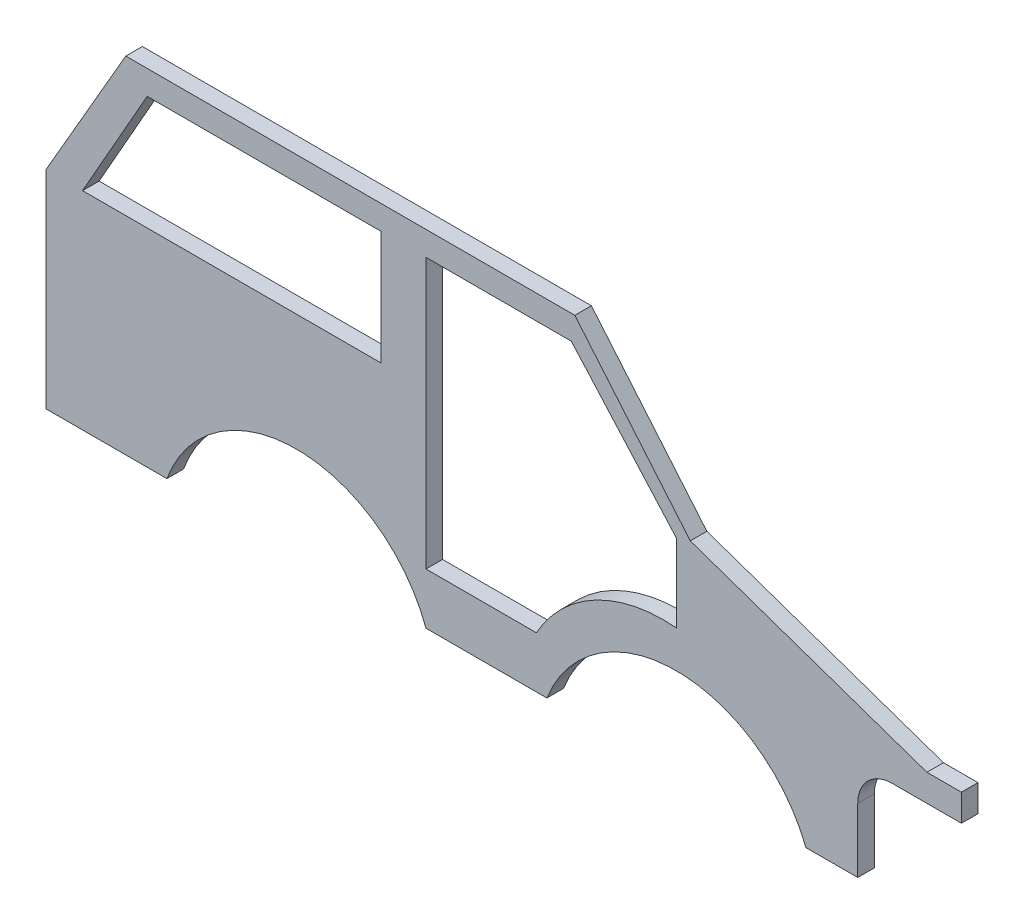
SolidWorks part; units mm, degrees
ref_plane "Alzado" through (0, 0, 0) normal (0, 0, 1) x (1, 0, 0)
ref_plane "Planta" through (0, 0, 0) normal (0, 1, 0) x (1, 0, 0)
ref_plane "Vista lateral" through (0, 0, 0) normal (1, 0, 0) x (0, 0, -1)
sketch "Croquis1" plane through (0, 0, 0) normal (0, 0, 1) x (1, 0, 0)
  line L0 (-17.5, 0) -> (17.5, 0)
  line L1 (-17.5, 0) -> (-92.5, 0) construction
  line L2 (-92.5, 0) -> (-127.5, 0)
  line L3 (17.5, 0) -> (92.5, 0) construction
  line L4 (-127.5, 0) -> (-127.5, 60)
  line L5 (-127.5, 60) -> (-104.406, 100)
  line L6 (-104.406, 100) -> (25.594, 100)
  line L7 (25.594, 100) -> (59.019, 60.1657)
  line L8 (92.5, 0) -> (92.5, 33) construction
  line L15 (59.019, 60.1657) -> (127.5131, 36.4)
  line L16 (-55, 0) -> (-55, 25) construction
  line L17 (55, 0) -> (55, 25) construction
  line L18 (-116.917, 60) -> (-98.2057, 92.999)
  line L19 (-98.2057, 92.999) -> (-30.4889, 92.999)
  line L20 (-30.4889, 92.999) -> (-30.4889, 60)
  line L21 (-30.4889, 60) -> (-116.917, 60)
  line L30 (92.5, 0) -> (107.5, 0)
  line L39 (137.5131, 28.6) -> (137.5131, 36.4)
  line L40 (137.5131, 36.4) -> (127.5131, 36.4)
  line L44 (107.5, 0) -> (107.5, 18.6)
  line L46 (-17.5, 92.999) -> (-17.5, 14.8474)
  line L47 (-17.5, 14.8474) -> (14.4667, 14.8474)
  line L48 (-17.5, 92.999) -> (24.5788, 92.999)
  line L49 (24.5788, 92.999) -> (55, 58.8607)
  line L50 (55, 58.8607) -> (55, 36.3213)
  line L51 (117.5, 28.6) -> (137.5131, 28.6)
  arc A0 (-92.5, 0) -> (-17.5, 0) centre (-55, -13.7734) cw
  arc A1 (17.5, 0) -> (92.5, 0) centre (55, -14.6968) cw
  arc A4 (107.5, 18.6) -> (117.5, 28.6) centre (117.5, 18.6) cw
  arc A5 (55, 36.3213) -> (14.4667, 14.8474) centre (51.2398, -5.5728) ccw
  point P4 (0, 0)
  dimension "D14" = 10
  dimension "D1" = 35
  dimension "D2" = 35
  dimension "D3" = 75
  dimension "D4" = 75
  dimension "D5" = 210
  dimension "D6" = 60
  dimension "D7" = 40
  dimension "D8" = 52
  dimension "D9" = 230
  dimension "D10" = 15
  dimension "D11" = 10
  dimension "D12" = 130
  dimension "D13" = 7.8
  dimension "D15" = 72.5
extrude "Saliente-Extruir2" add sketch "Croquis1" along normal blind 4.8
